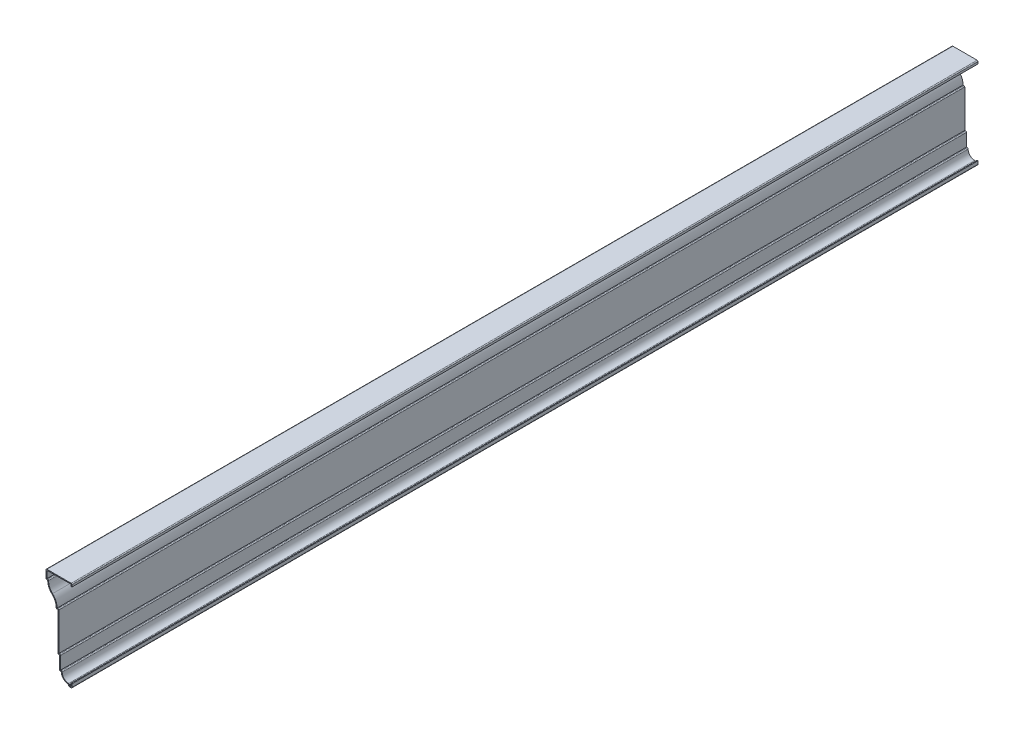
SolidWorks part; units mm, degrees
ref_plane "Front Plane" through (0, 0, 0) normal (0, 0, 1) x (1, 0, 0)
ref_plane "Top Plane" through (0, 0, 0) normal (0, 1, 0) x (1, 0, 0)
ref_plane "Right Plane" through (0, 0, 0) normal (1, 0, 0) x (0, 0, -1)
sketch "Sketch1" plane through (0, 0, 0) normal (0, 0, 1) x (1, 0, 0)
  line L0 (0, 0) -> (0, 140.0709) construction
  line L1 (0, 123.0313) -> (0, 127)
  line L2 (0, 127) -> (-36.5125, 127)
  line L3 (-36.5125, 127) -> (-36.5125, 114.3)
  line L4 (-36.5125, 114.3) -> (-34.1312, 114.3)
  line L5 (0, 5.5562) -> (0, 0)
  line L6 (0, 0) -> (-4.7625, 0)
  line L7 (-4.7625, 0) -> (-4.7625, 2.3812)
  line L8 (-15.0813, 12.7) -> (-17.4625, 12.7)
  line L9 (-17.4625, 12.7) -> (-17.4625, 31.75)
  line L10 (-17.4625, 31.75) -> (-19.8438, 31.75)
  line L11 (-19.8438, 31.75) -> (-19.8438, 85.725)
  line L12 (-19.8438, 85.725) -> (-22.225, 85.725)
  arc A0 (-4.7625, 2.3812) -> (-15.0813, 12.7) centre (-4.7625, 12.7) cw
  arc A1 (-34.1312, 114.3) -> (-28.1617, 100.3963) centre (-15.8793, 113.9031) ccw
  arc A2 (-28.1617, 100.3963) -> (-22.225, 85.725) centre (-40.4441, 86.8895) cw
  point P21 (0, 0)
  point P22 (-15.8751, 114.3)
  point P23 (-28.1988, 99.5281)
  dimension "D6" = 10.3187
  dimension "D12" = 18.2562
  dimension "D1" = 127
  dimension "D2" = 3.9688
  dimension "D3" = 5.5562
  dimension "D4" = 4.7625
  dimension "D5" = 2.3813
  dimension "D7" = 2.3813
  dimension "D8" = 19.05
  dimension "D9" = 53.975
  dimension "D10" = 12.7
  dimension "D11" = 36.5125
  dimension "D13" = 0.3969
extrude "Extrude-Thin1" add sketch "Sketch1" against normal blind 1270 thin thin type one direction wall 1.27
fillet "Fillet1" radius 1.27 13 edges at (0, 0, -635) (-4.7625, 0, -635) (-3.4925, 3.7408, -635) (-13.7217, 13.97, -635) (-17.4625, 12.7, -635) (-16.1925, 33.02, -635) (-19.8438, 31.75, -635) (-18.5738, 86.995, -635) (-22.225, 85.725, -635) (0, 127, -635) (-36.5125, 114.3, -635) (-32.7836, 115.57, -635) (-36.5125, 127, -635)
